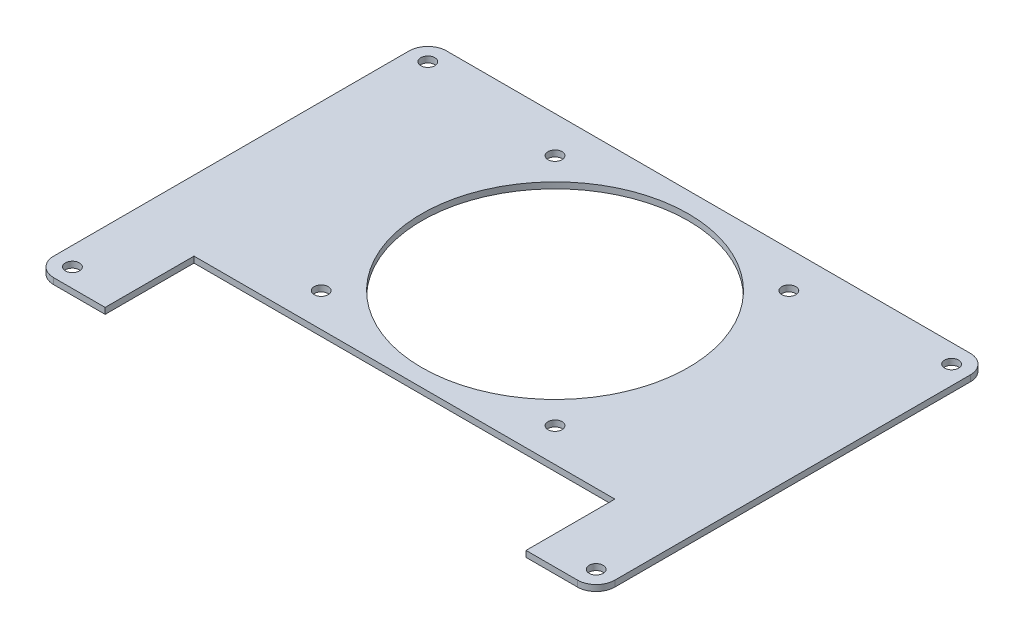
SolidWorks part; units mm, degrees
ref_plane "Front Plane" through (0, 0, 0) normal (0, 0, 1) x (1, 0, 0)
ref_plane "Top Plane" through (0, 0, 0) normal (0, 1, 0) x (1, 0, 0)
ref_plane "Right Plane" through (0, 0, 0) normal (1, 0, 0) x (0, 0, -1)
sketch "Sketch1" plane through (0, 0, 0) normal (0, 1, 0) x (1, 0, 0)
  line L1 (-56, -42) -> (56, -42)
  line L2 (-60, -38) -> (-60, 38)
  line L3 (-56, 42) -> (56, 42)
  line L4 (60, -38) -> (60, 38)
  line L5 (-58.6127, -41.0289) -> (58.6127, 41.0289) construction
  line L6 (-58.6127, 41.0289) -> (58.6127, -41.0289) construction
  arc A0 (-56, 42) -> (-60, 38) centre (-56, 38) ccw
  arc A1 (60, 38) -> (56, 42) centre (56, 38) ccw
  arc A2 (56, -42) -> (60, -38) centre (56, -38) ccw
  arc A3 (-60, -38) -> (-56, -42) centre (-56, -38) ccw
  circle A4 centre (-56, 38) radius 1.5
  circle A5 centre (56, 38) radius 1.5
  circle A6 centre (56, -38) radius 1.5
  circle A7 centre (-56, -38) radius 1.5
  point P0 (0, 0)
  dimension "D3" = 8
  dimension "D1" = 3
  dimension "D2" = 3
  dimension "D6" = 3
  dimension "D7" = 3
  dimension "D4" = 2
  dimension "D5" = 2
extrude "Boss-Extrude1" add sketch "Sketch1" along normal blind 1.3
sketch "Sketch2" plane through (0, 1.3, 0) normal (0, 1, 0) x (1, 0, 0)
  line L0 (60, -38) -> (60, 38) construction
  line L1 (-45, -42) -> (45, -42)
  line L3 (-45, -23) -> (45, -23)
  line L5 (56, 42) -> (-56, 42) construction
  line L10 (45, -23) -> (45, -42)
  line L14 (-45, -23) -> (-45, -42)
  circle A0 centre (0, 9.2) radius 28.5
  circle A1 centre (-25, 34.2) radius 1.5
  circle A2 centre (25, 34.2) radius 1.5
  circle A3 centre (25, -15.8) radius 1.5
  circle A4 centre (-25, -15.8) radius 1.5
  dimension "D2" = 57
  dimension "D3" = 32.8
  dimension "D4" = 25
  dimension "D5" = 25
  dimension "D6" = 3
  dimension "D1" = 19
  dimension "D9" = 15
  dimension "D7" = 2
  dimension "D8" = 2
extrude "Cut-Extrude1" cut sketch "Sketch2" against normal blind 10
